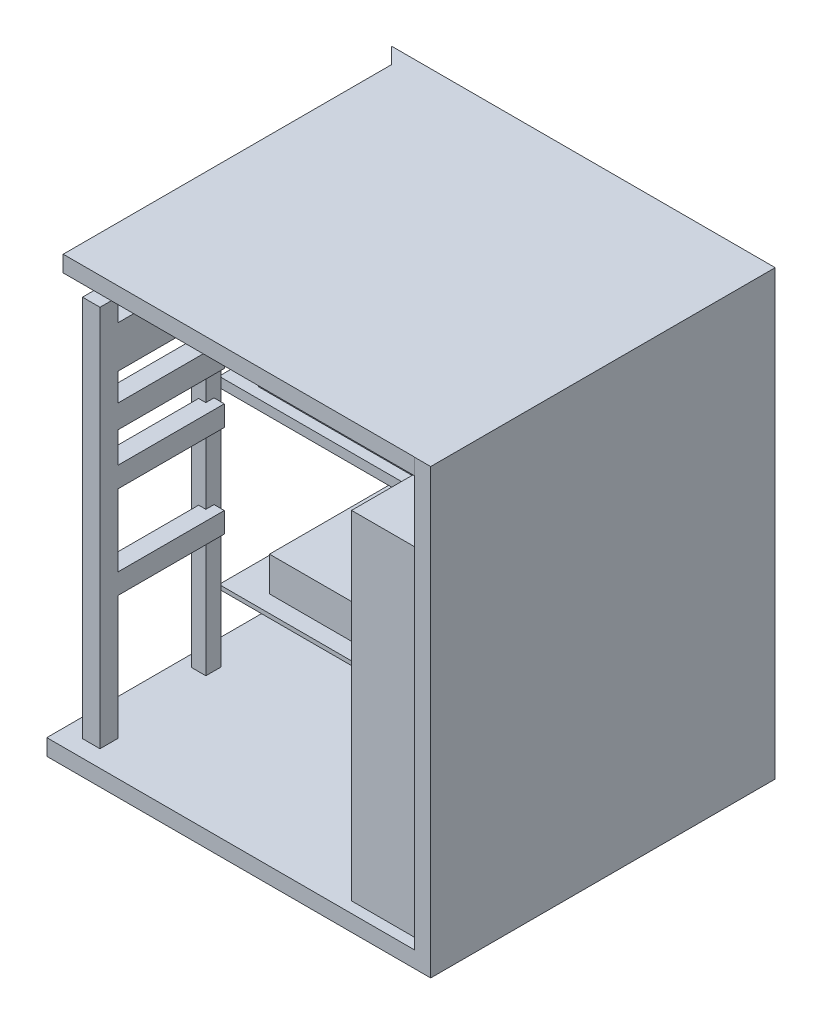
SolidWorks part; units mm, degrees
ref_plane "Front Plane" through (0, 0, 0) normal (0, 0, 1) x (1, 0, 0)
ref_plane "Top Plane" through (0, 0, 0) normal (0, 1, 0) x (1, 0, 0)
ref_plane "Right Plane" through (0, 0, 0) normal (1, 0, 0) x (0, 0, -1)
sketch "Sketch1" plane through (0, 0, 0) normal (0, 1, 0) x (1, 0, 0)
  line L1 (0, 0) -> (2377.44, 0)
  line L2 (0, 0) -> (0, 2133.6)
  line L3 (0, 2133.6) -> (2377.44, 2133.6)
  line L4 (2377.44, 0) -> (2377.44, 2133.6)
  dimension "D1" = 2377.44
  dimension "D2" = 2133.6
extrude "Boss-Extrude1" add sketch "Sketch1" along normal blind 100.584
sketch "Sketch2" plane through (0, 0, 0) normal (0, 1, 0) x (1, 0, 0)
  line L0 (2377.44, 2133.6) -> (0, 2133.6) construction
  line L3 (0, 2133.6) -> (100.584, 2133.6)
  line L5 (0, 2133.6) -> (100.584, 2033.016)
  line L6 (2377.44, 2133.6) -> (100.584, 2133.6)
  line L7 (2377.44, 2133.6) -> (2377.44, 2033.016)
  line L8 (2276.856, 2033.016) -> (100.584, 2033.016)
  line L10 (2377.44, 0) -> (2276.856, 0)
  line L11 (2377.44, 0) -> (2377.44, 2033.016)
  line L13 (2276.856, 0) -> (2276.856, 2033.016)
  dimension "D2" = 100.584
  dimension "D3" = 100.584
extrude "Boss-Extrude2" add sketch "Sketch2" along normal blind 2743.2
sketch "Sketch3" plane through (0, 0, -2033.016) normal (0, 0, 1) x (1, 0, 0)
  line L1 (100.584, 2743.2) -> (2276.856, 2743.2)
  line L2 (100.584, 2743.2) -> (100.584, 2642.616)
  line L3 (100.584, 2642.616) -> (2276.856, 2642.616)
  line L4 (2276.856, 2743.2) -> (2276.856, 2642.616)
  line L5 (100.584, 2743.2) -> (2276.856, 2743.2) construction
  dimension "D1" = 100.584
  dimension "D2" = 0
extrude "Boss-Extrude3" add sketch "Sketch3" along normal blind 2032.0102
sketch "Sketch4" plane through (0, 0, -2033.016) normal (0, 0, 1) x (1, 0, 0)
  line L0 (100.584, 2642.616) -> (2276.856, 2642.616) construction
  line L1 (100.584, 489.4868) -> (2276.856, 489.4868)
  line L2 (100.584, 489.4868) -> (100.584, 464.0727)
  line L3 (100.584, 464.0727) -> (2276.856, 464.0727)
  line L4 (2276.856, 489.4868) -> (2276.856, 464.0727)
  line L5 (2276.856, 2642.616) -> (2276.856, 100.584) construction
  line L7 (2276.856, 1545.6554) -> (100.584, 1545.6554)
  line L8 (2276.856, 1545.6554) -> (2276.856, 1606.296)
  line L9 (2276.856, 1606.296) -> (100.584, 1606.296)
  line L10 (100.584, 1545.6554) -> (100.584, 1606.296)
  dimension "D1" = 1036.32
extrude "Boss-Extrude4" add sketch "Sketch4" along normal blind 1066.8
sketch "Sketch5" plane through (2276.856, 0, 0) normal (-1, 0, 0) x (0, 0, 1)
  line L0 (-2033.016, 100.584) -> (0, 100.584) construction
  line L1 (-878.4922, 100.584) -> (-67.7483, 100.584)
  line L2 (-878.4922, 100.584) -> (-878.4922, 2195.4114)
  line L3 (-878.4922, 2195.4114) -> (-67.7483, 2195.4114)
  line L4 (-67.7483, 100.584) -> (-67.7483, 2195.4114)
extrude "Boss-Extrude5" add sketch "Sketch5" along normal blind 457.2
sketch "Sketch6" plane through (0, 1606.296, 0) normal (0, 1, 0) x (1, 0, 0)
  line L1 (2276.856, 2033.016) -> (279.1526, 2033.016)
  line L2 (2276.856, 2033.016) -> (2276.856, 1031.5858)
  line L3 (2276.856, 1031.5858) -> (279.1526, 1031.5858)
  line L4 (279.1526, 2033.016) -> (279.1526, 1031.5858)
extrude "Boss-Extrude6" add sketch "Sketch6" along normal blind 213.36
sketch "Sketch7" plane through (0, 489.4868, 0) normal (0, 1, 0) x (1, 0, 0)
  line L1 (2276.856, 2033.016) -> (307.7562, 2033.016)
  line L2 (2276.856, 2033.016) -> (2276.856, 1071.3233)
  line L3 (2276.856, 1071.3233) -> (307.7562, 1071.3233)
  line L4 (307.7562, 2033.016) -> (307.7562, 1071.3233)
extrude "Boss-Extrude7" add sketch "Sketch7" along normal blind 213.36
sketch "Sketch8" plane through (0, 1819.656, 0) normal (0, 1, 0) x (1, 0, 0)
  line L1 (2109.6038, 1896.0279) -> (1842.7413, 1896.0279)
  line L2 (2109.6038, 1896.0279) -> (2109.6038, 1253.7574)
  line L3 (2109.6038, 1253.7574) -> (1842.7413, 1253.7574)
  line L4 (1842.7413, 1896.0279) -> (1842.7413, 1253.7574)
extrude "Boss-Extrude8" add sketch "Sketch8" along normal blind 100.584
sketch "Sketch9" plane through (0, 702.8468, 0) normal (0, 1, 0) x (1, 0, 0)
  line L1 (2142.9022, 1839.2764) -> (1807.785, 1839.2764)
  line L2 (2142.9022, 1839.2764) -> (2142.9022, 1250.2152)
  line L3 (2142.9022, 1250.2152) -> (1807.785, 1250.2152)
  line L4 (1807.785, 1839.2764) -> (1807.785, 1250.2152)
extrude "Boss-Extrude9" add sketch "Sketch9" along normal blind 100.584
sketch "Sketch10" plane through (0, 100.584, 0) normal (0, 1, 0) x (1, 0, 0)
  line L1 (71.3308, 919.2777) -> (160.9178, 919.2777)
  line L2 (71.3308, 919.2777) -> (71.3308, 824.1575)
  line L3 (71.3308, 824.1575) -> (160.9178, 824.1575)
  line L4 (160.9178, 919.2777) -> (160.9178, 824.1575)
  line L5 (116.1243, 217.7467) -> (224.4399, 217.7467)
  line L6 (116.1243, 217.7467) -> (116.1243, 104.9121)
  line L7 (116.1243, 104.9121) -> (224.4399, 104.9121)
  line L8 (224.4399, 217.7467) -> (224.4399, 104.9121)
extrude "Boss-Extrude10" add sketch "Sketch10" along normal blind 2368.042
sketch "Sketch11" plane through (0, 0, -217.7467) normal (0, 0, -1) x (-1, 0, 0)
  line L0 (-116.1243, 2468.626) -> (-116.1243, 100.584) construction
  line L1 (-116.1243, 993.366) -> (-224.4399, 993.366)
  line L2 (-116.1243, 993.366) -> (-116.1243, 867.0357)
  line L3 (-116.1243, 867.0357) -> (-224.4399, 867.0357)
  line L4 (-224.4399, 993.366) -> (-224.4399, 867.0357)
  line L5 (-224.4399, 2468.626) -> (-224.4399, 100.584) construction
  line L7 (-116.1243, 1438.7783) -> (-224.4399, 1438.7783)
  line L8 (-116.1243, 1438.7783) -> (-116.1243, 1565.6438)
  line L9 (-116.1243, 1565.6438) -> (-224.4399, 1565.6438)
  line L10 (-224.4399, 1438.7783) -> (-224.4399, 1565.6438)
  line L11 (-116.1243, 1755.4068) -> (-224.4399, 1755.4068)
  line L12 (-116.1243, 1755.4068) -> (-116.1243, 1899.2235)
  line L13 (-116.1243, 1899.2235) -> (-224.4399, 1899.2235)
  line L14 (-224.4399, 1755.4068) -> (-224.4399, 1899.2235)
  line L15 (-116.1243, 2069.8496) -> (-224.4399, 2069.8496)
  line L16 (-116.1243, 2069.8496) -> (-116.1243, 2329.8705)
  line L17 (-116.1243, 2329.8705) -> (-224.4399, 2329.8705)
  line L18 (-224.4399, 2069.8496) -> (-224.4399, 2329.8705)
extrude "Boss-Extrude11" add sketch "Sketch11" along normal blind 657.098
